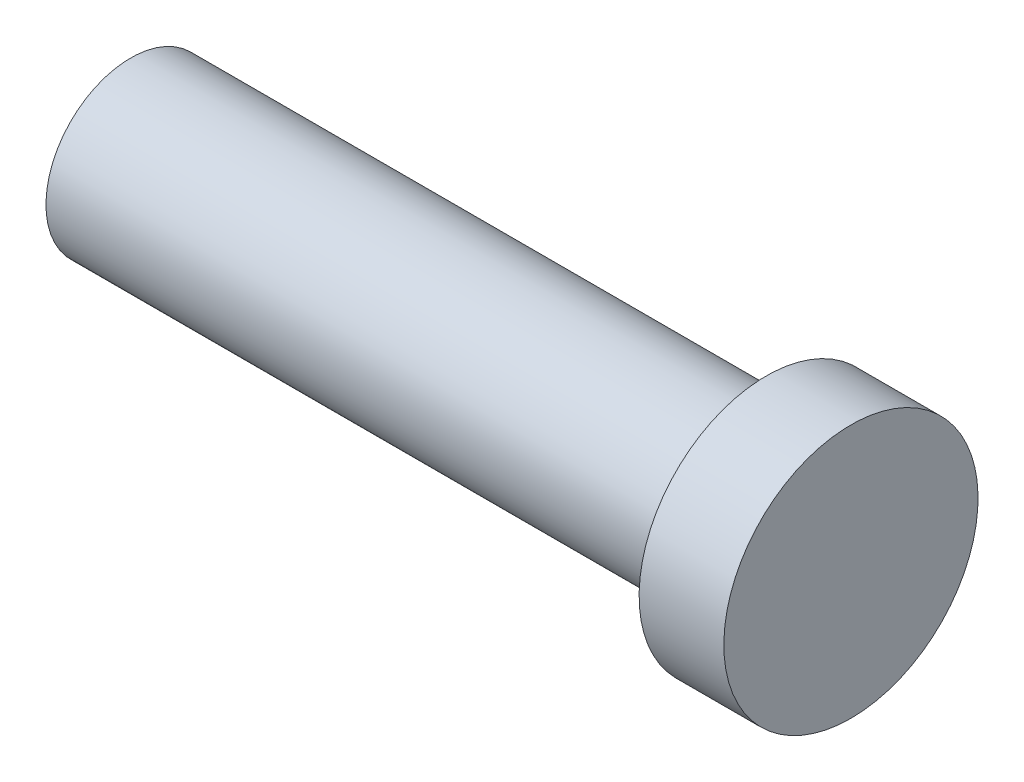
SolidWorks part; units mm, degrees
ref_plane "Front Plane" through (0, 0, 0) normal (0, 0, 1) x (1, 0, 0)
ref_plane "Top Plane" through (0, 0, 0) normal (0, 1, 0) x (1, 0, 0)
ref_plane "Right Plane" through (0, 0, 0) normal (1, 0, 0) x (0, 0, -1)
sketch "Sketch1" plane through (0, 0, 0) normal (0, 0, 1) x (1, 0, 0)
  line L0 (-17, 0) -> (0, 0) construction
  line L1 (0, 0) -> (-17, 0)
  line L2 (0, 0) -> (0, 2)
  line L3 (-2, 2) -> (-17, 2)
  line L4 (-17, 0) -> (-17, 2)
  line L5 (0, 0) -> (-4.2963, 0)
  line L6 (0, 0) -> (0, 3)
  line L7 (0, 3) -> (-2, 3)
  line L8 (-2, 2) -> (-2, 3)
  dimension "D1" = 2
  dimension "D2" = 2
  dimension "D3" = 15
  dimension "D4" = 3
revolve "Revolve1" add sketch "Sketch1" angle 360 about L0
